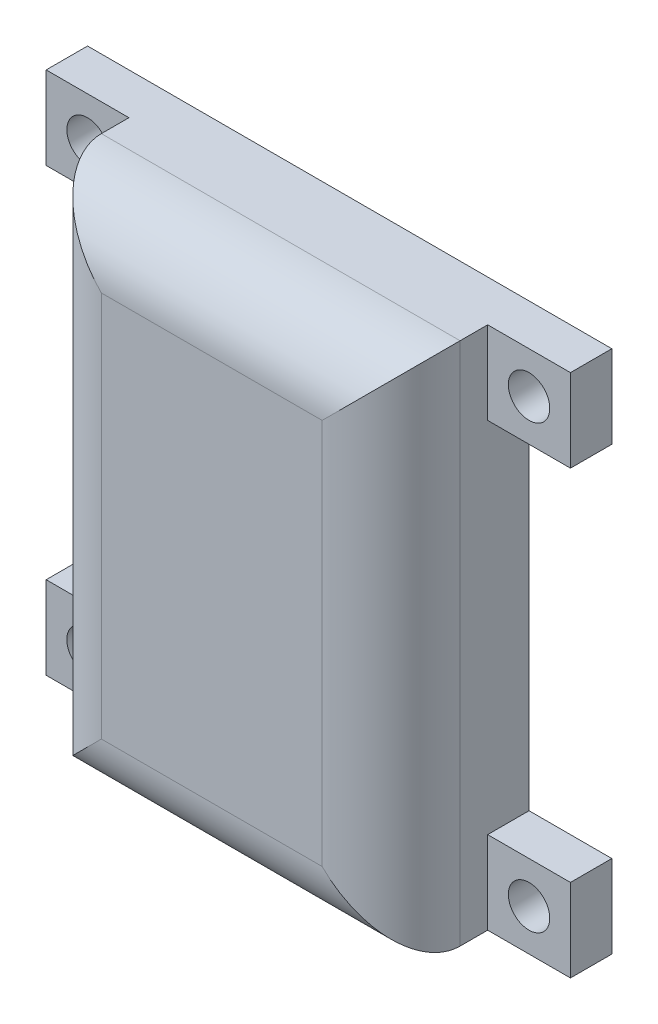
SolidWorks part; units mm, degrees
ref_plane "正面" through (0, 0, 0) normal (0, 0, 1) x (1, 0, 0)
ref_plane "平面" through (0, 0, 0) normal (0, 1, 0) x (1, 0, 0)
ref_plane "右側面" through (0, 0, 0) normal (1, 0, 0) x (0, 0, -1)
sketch "ｽｹｯﾁ1" plane through (0, 0, 0) normal (0, 0, 1) x (1, 0, 0)
  line L1 (13, -19) -> (-13, -19)
  line L2 (13, -19) -> (13, 19)
  line L3 (13, 19) -> (-13, 19)
  line L4 (-13, -19) -> (-13, 19)
  line L5 (13, -19) -> (-13, 19) construction
  line L6 (13, 19) -> (-13, -19) construction
  point P0 (0, 0)
  dimension "D1" = 38
  dimension "D2" = 26
extrude "ﾎﾞｽ - 押し出し1" add sketch "ｽｹｯﾁ1" along normal blind 10
sketch "ｽｹｯﾁ2" plane through (0, 0, 0) normal (0, 0, 1) x (1, 0, 0)
  line L1 (11, -17) -> (-11, -17)
  line L2 (11, -17) -> (11, 17)
  line L3 (11, 17) -> (-11, 17)
  line L4 (-11, -17) -> (-11, 17)
  line L5 (11, -17) -> (-11, 17) construction
  line L6 (11, 17) -> (-11, -17) construction
  point P0 (0, 0)
  dimension "D1" = 22
  dimension "D2" = 34
extrude "ｶｯﾄ - 押し出し1" cut sketch "ｽｹｯﾁ2" along normal blind 8
sketch "ｽｹｯﾁ3" plane through (0, 0, 0) normal (0, 0, 1) x (1, 0, 0)
  line L0 (13, 19) -> (-13, 19) construction
  line L1 (-0.8522, 2) -> (1.1478, 2)
  line L2 (-0.8522, 2) -> (-0.8522, 9)
  line L3 (-0.8522, 9) -> (1.1478, 9)
  line L4 (1.1478, 2) -> (1.1478, 9)
  line L5 (-0.8522, 2) -> (1.1478, 9) construction
  line L6 (-0.8522, 9) -> (1.1478, 2) construction
  point P0 (0.1478, 5.5)
  dimension "D1" = 7
  dimension "D2" = 2
  dimension "D3" = 10
sketch "ｽｹｯﾁ4" plane through (0, 0, 0) normal (0, 0, 1) x (1, 0, 0)
  line L0 (13, -19) -> (13, 19) construction
  line L1 (13, 19) -> (19, 19)
  line L2 (13, 19) -> (13, 13)
  line L3 (13, 13) -> (19, 13)
  line L4 (19, 19) -> (19, 13)
  line L5 (13, -19) -> (19, -19)
  line L6 (13, -19) -> (13, -13)
  line L7 (13, -13) -> (19, -13)
  line L8 (19, -19) -> (19, -13)
  line L9 (-13, -19) -> (13, -19) construction
  line L10 (-13, -19) -> (-19, -19)
  line L11 (-13, -19) -> (-13, -13)
  line L12 (-13, -13) -> (-19, -13)
  line L13 (-19, -19) -> (-19, -13)
  line L14 (-13, 19) -> (-19, 19)
  line L15 (-13, 19) -> (-13, 13)
  line L16 (-13, 13) -> (-19, 13)
  line L17 (-19, 19) -> (-19, 13)
  dimension "D1" = 6
  dimension "D2" = 6
  dimension "D3" = 6
  dimension "D4" = 6
  dimension "D5" = 6
  dimension "D6" = 6
  dimension "D7" = 6
  dimension "D8" = 6
  dimension "D9" = 0
extrude "ﾎﾞｽ - 押し出し2" add sketch "ｽｹｯﾁ4" along normal blind 3
sketch "ｽｹｯﾁ5" plane through (0, 0, 0) normal (0, 0, 1) x (1, 0, 0)
  line L0 (-13, 19) -> (-19, 19) construction
  line L1 (-19, 19) -> (-19, 13) construction
  line L2 (-13, -13) -> (-19, -13) construction
  line L3 (19, -19) -> (19, -13) construction
  line L4 (-19, -13) -> (-19, -19) construction
  line L5 (19, -13) -> (13, -13) construction
  line L6 (19, 13) -> (19, 19) construction
  line L7 (19, 19) -> (13, 19) construction
  circle A0 centre (-16, 16) radius 1.5
  circle A1 centre (-16, -16) radius 1.5
  circle A2 centre (16, -16) radius 1.5
  circle A3 centre (16, 16) radius 1.5
  dimension "D1" = 3
  dimension "D2" = 3
  dimension "D3" = 3
  dimension "D4" = 3
  dimension "D5" = 3
  dimension "D6" = 3
  dimension "D7" = 3
  dimension "D8" = 3
  dimension "D9" = 3
  dimension "D10" = 3
  dimension "D11" = 3
  dimension "D12" = 3
extrude "ｶｯﾄ - 押し出し4" cut sketch "ｽｹｯﾁ5" along normal through all
fillet "ﾌｨﾚｯﾄ1" radius 5 4 edges at (0, 19, 10) (0, -19, 10) (13, 0, 10) (-13, 0, 10)
